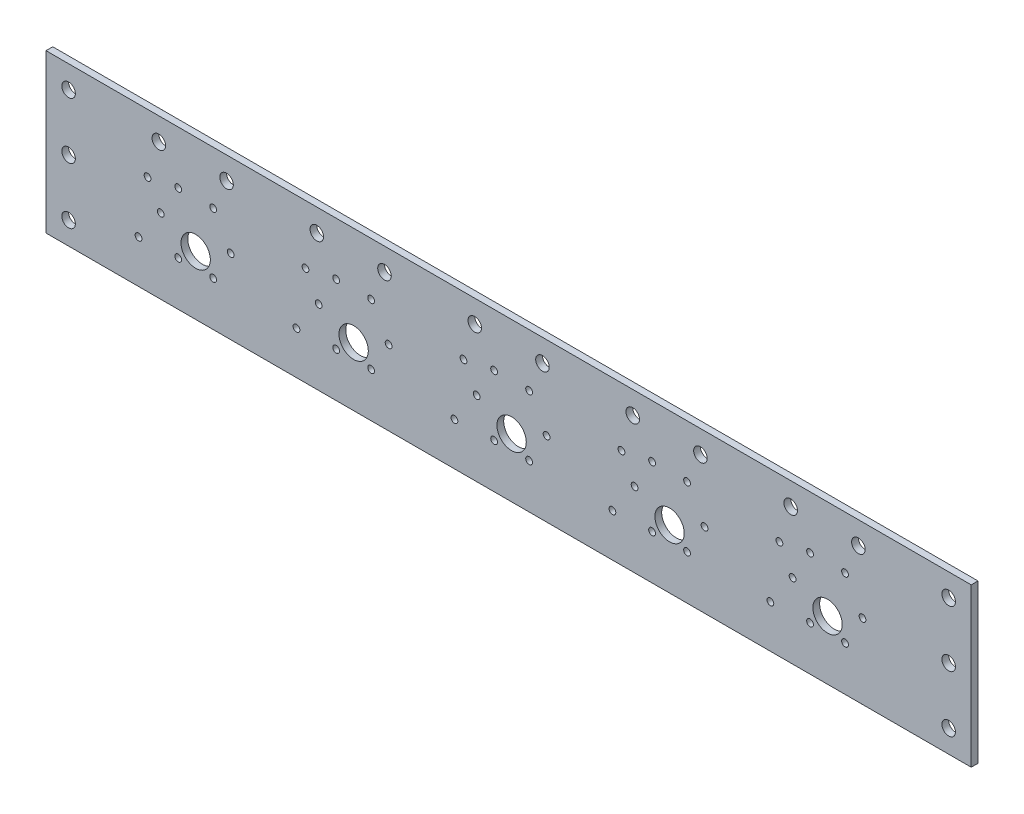
SolidWorks part; units mm, degrees
material "普通碳钢"
ref_plane "前视基准面" through (0, 0, 0) normal (0, 0, 1) x (1, 0, 0)
ref_plane "上视基准面" through (0, 0, 0) normal (0, 1, 0) x (1, 0, 0)
ref_plane "右视基准面" through (0, 0, 0) normal (1, 0, 0) x (0, 0, -1)
sketch "草图1" plane through (0, 0, 0) normal (0, 0, 1) x (1, 0, 0)
  line L0 (-15.1749, 60) -> (200.6803, 60) construction
  line L1 (0, 0) -> (410, 0)
  line L2 (0, 0) -> (0, 70)
  line L3 (0, 70) -> (410, 70)
  line L4 (410, 0) -> (410, 70)
  line L5 (80, 60) -> (80, 39.4084) construction
  line L6 (66.3269, 26.1578) -> (66.3269, 43.666) construction
  line L7 (80, 60) -> (61.142, 13.3248) construction
  line L8 (50.8269, 33.1578) -> (81.8269, 33.1578) construction
  line L9 (325, 44) -> (325, 19) construction
  line L10 (325, 19) -> (304.2127, 19) construction
  line L11 (66.3269, 33.1578) -> (74.0769, 19.7344) construction
  line L12 (0, 35) -> (33.6998, 35) construction
  line L13 (10, 60) -> (10, 10) construction
  line L14 (400, 60) -> (400, 10) construction
  line L15 (410, 35) -> (389.9044, 35) construction
  circle A0 centre (10, 60) radius 3
  circle A1 centre (50, 60) radius 3
  circle A2 centre (80, 60) radius 3
  circle A3 centre (120, 60) radius 3
  circle A4 centre (150, 60) radius 3
  circle A5 centre (190, 60) radius 3
  circle A6 centre (220, 60) radius 3
  circle A7 centre (260, 60) radius 3
  circle A8 centre (290, 60) radius 3
  circle A9 centre (330, 60) radius 3
  circle A10 centre (360, 60) radius 3
  circle A11 centre (400, 60) radius 3
  circle A12 centre (66.3269, 26.1578) radius 6.5
  circle A13 centre (136.3269, 26.1578) radius 6.5
  circle A14 centre (206.3269, 26.1578) radius 6.5
  circle A15 centre (276.3269, 26.1578) radius 6.5
  circle A16 centre (346.3269, 26.1578) radius 6.5
  circle A17 centre (66.3269, 33.1578) radius 15.5 construction
  circle A18 centre (81.8269, 33.1578) radius 1.5
  circle A19 centre (74.0769, 19.7344) radius 1.5
  circle A20 centre (58.5769, 19.7344) radius 1.5
  circle A21 centre (50.8269, 33.1578) radius 1.5
  circle A22 centre (58.5769, 46.5812) radius 1.5
  circle A23 centre (74.0769, 46.5812) radius 1.5
  circle A24 centre (128.5769, 46.5812) radius 1.5
  circle A25 centre (120.8269, 33.1578) radius 1.5
  circle A26 centre (128.5769, 19.7344) radius 1.5
  circle A27 centre (144.0769, 19.7344) radius 1.5
  circle A28 centre (144.0769, 46.5812) radius 1.5
  circle A29 centre (151.8269, 33.1578) radius 1.5
  circle A30 centre (198.5769, 46.5812) radius 1.5
  circle A31 centre (190.8269, 33.1578) radius 1.5
  circle A32 centre (198.5769, 19.7344) radius 1.5
  circle A33 centre (214.0769, 19.7344) radius 1.5
  circle A34 centre (214.0769, 46.5812) radius 1.5
  circle A35 centre (221.8269, 33.1578) radius 1.5
  circle A36 centre (268.5769, 46.5812) radius 1.5
  circle A37 centre (260.8269, 33.1578) radius 1.5
  circle A38 centre (268.5769, 19.7344) radius 1.5
  circle A39 centre (284.0769, 19.7344) radius 1.5
  circle A40 centre (284.0769, 46.5812) radius 1.5
  circle A41 centre (291.8269, 33.1578) radius 1.5
  circle A42 centre (338.5769, 46.5812) radius 1.5
  circle A43 centre (330.8269, 33.1578) radius 1.5
  circle A44 centre (338.5769, 19.7344) radius 1.5
  circle A45 centre (354.0769, 19.7344) radius 1.5
  circle A46 centre (354.0769, 46.5812) radius 1.5
  circle A47 centre (361.8269, 33.1578) radius 1.5
  circle A48 centre (325, 44) radius 1.5
  circle A49 centre (321, 19) radius 1.5
  circle A50 centre (255, 44) radius 1.5
  circle A51 centre (251, 19) radius 1.5
  circle A52 centre (185, 44) radius 1.5
  circle A53 centre (181, 19) radius 1.5
  circle A54 centre (115, 44) radius 1.5
  circle A55 centre (111, 19) radius 1.5
  circle A56 centre (45, 44) radius 1.5
  circle A57 centre (41, 19) radius 1.5
  circle A58 centre (400, 10) radius 3
  circle A59 centre (10, 10) radius 3
  circle A60 centre (10, 35) radius 3
  circle A61 centre (400, 35) radius 3
  point P42 (66.3269, 33.1578)
  point P63 (66.3269, 33.1578)
  dimension "D3" = 6
  dimension "D4" = 6
  dimension "D9" = 13
  dimension "D14" = 7
  dimension "D15" = 6
  dimension "D16" = 3
  dimension "D17" = 31
  dimension "D19" = 3
  dimension "D23" = 3
  dimension "D24" = 4
  dimension "D26" = 5
  dimension "D27" = 6
  dimension "D28" = 6
  dimension "D1" = 410
  dimension "D2" = 70
  dimension "D5" = 40
  dimension "D6" = 10
  dimension "D7" = 10
  dimension "D10" = 22
  dimension "D11" = 36.5
  dimension "D13" = 70
  dimension "D20" = 25
  dimension "D21" = 26
  dimension "D22" = 85
  dimension "D25" = 60
  dimension "D8" = 6
  dimension "D12" = 5
  dimension "D18" = 5
extrude "凸台-拉伸1" add sketch "草图1" along normal blind 3
